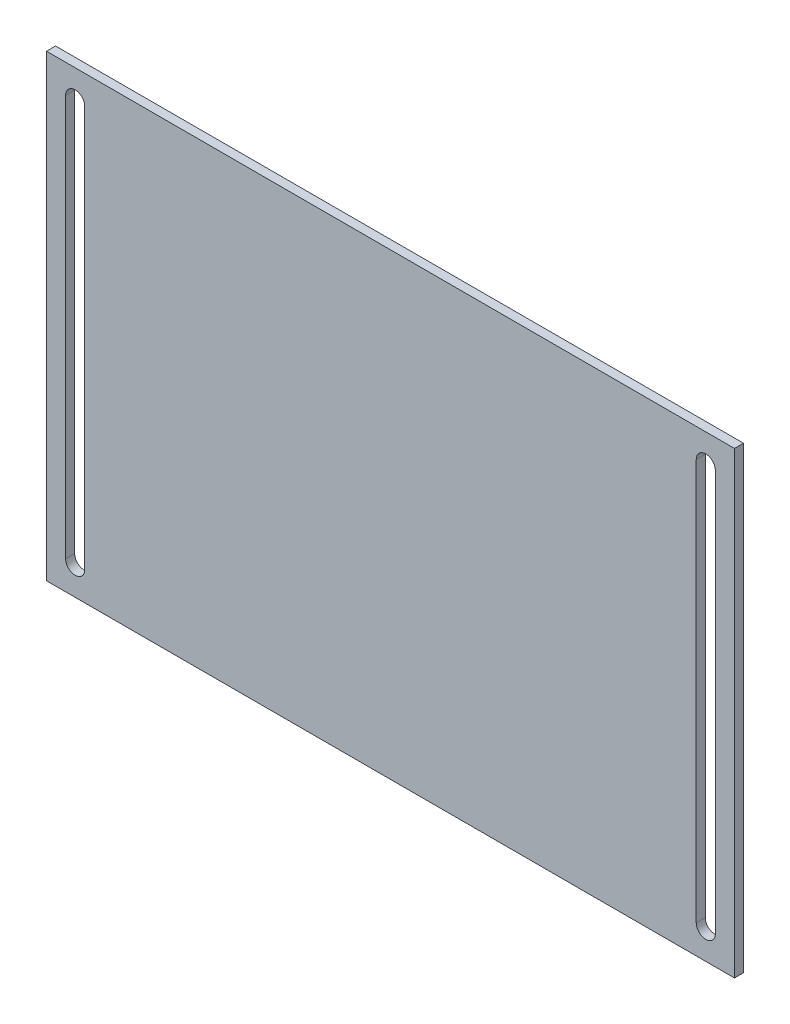
SolidWorks part; units mm, degrees
ref_plane "Front" through (0, 0, 0) normal (0, 0, 1) x (1, 0, 0)
ref_plane "Top" through (0, 0, 0) normal (0, 1, 0) x (1, 0, 0)
ref_plane "Right" through (0, 0, 0) normal (1, 0, 0) x (0, 0, -1)
sketch "Sketch1" plane through (0, 0, 0) normal (0, 0, 1) x (1, 0, 0)
  line L0 (-104.775, 66.675) -> (-104.775, -66.675) construction
  line L1 (114.3, -76.2) -> (-114.3, -76.2)
  line L2 (114.3, -76.2) -> (114.3, 76.2)
  line L3 (114.3, 76.2) -> (-114.3, 76.2)
  line L4 (-114.3, -76.2) -> (-114.3, 76.2)
  line L5 (114.3, -76.2) -> (-114.3, 76.2) construction
  line L6 (114.3, 76.2) -> (-114.3, -76.2) construction
  line L7 (-101.6, 66.675) -> (-101.6, -66.675)
  line L8 (-107.95, 66.675) -> (-107.95, -66.675)
  line L9 (104.775, 66.675) -> (104.775, -66.675) construction
  line L10 (107.95, 66.675) -> (107.95, -66.675)
  line L11 (101.6, 66.675) -> (101.6, -66.675)
  line L12 (-104.775, 0) -> (-114.3, 0) construction
  line L13 (104.775, 0) -> (114.3, 0) construction
  arc A0 (-101.6, 66.675) -> (-107.95, 66.675) centre (-104.775, 66.675) ccw
  arc A1 (-107.95, -66.675) -> (-101.6, -66.675) centre (-104.775, -66.675) ccw
  arc A2 (107.95, 66.675) -> (101.6, 66.675) centre (104.775, 66.675) ccw
  arc A3 (101.6, -66.675) -> (107.95, -66.675) centre (104.775, -66.675) ccw
  point P0 (0, 0)
  point P8 (-104.775, 0)
  point P13 (104.775, 0)
  dimension "D3" = 6.35
  dimension "D4" = 6.35
  dimension "D1" = 228.6
  dimension "D2" = 152.4
  dimension "D5" = 6.35
extrude "Boss-Extrude1" add sketch "Sketch1" along normal blind 3
